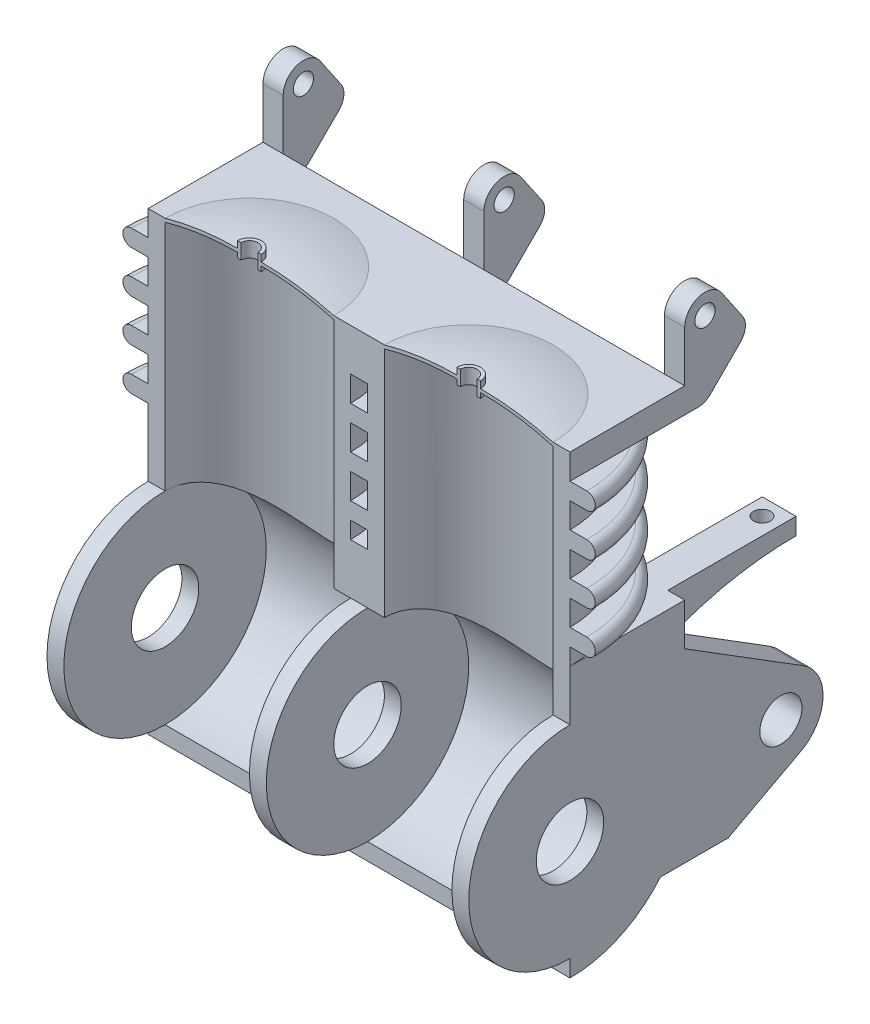
SolidWorks part; units mm, degrees
material "Plain Carbon Steel"
ref_plane "Front Plane" through (0, 0, 0) normal (0, 0, 1) x (1, 0, 0)
ref_plane "Top Plane" through (0, 0, 0) normal (0, 1, 0) x (1, 0, 0)
ref_plane "Right Plane" through (0, 0, 0) normal (1, 0, 0) x (0, 0, -1)
sketch "Sketch1" plane through (0, 0, 0) normal (1, 0, 0) x (0, 0, -1)
  line L1 (0, 160) -> (68, 160)
  line L2 (68, 160) -> (68, 86.6132)
  line L4 (0, 0) -> (0, 160)
  line L5 (0, 0) -> (70.0691, 0) construction
  arc A4 (0, 0) -> (68, 86.6132) centre (0, 70) ccw
  dimension "D3" = 70
  dimension "D1" = 160
  dimension "D2" = 68
extrude "Boss-Extrude1" add sketch "Sketch1" along normal mid plane 250
sketch "Sketch6" plane through (0, 0, 0) normal (0, 0, 1) x (1, 0, 0)
  line L0 (125, 160) -> (125, 170)
  line L3 (125, 195) -> (135, 195)
  line L7 (115, 267.9194) -> (115, 160)
  line L8 (115, 160) -> (125, 160)
  line L11 (125, 170) -> (135, 170)
  line L12 (135, 180) -> (125, 180)
  line L14 (135, 205) -> (125, 205)
  line L15 (65, 17.7772) -> (65, 302.2228) construction
  line L16 (125, 220) -> (135, 220)
  line L17 (135, 230) -> (125, 230)
  line L18 (125, 160) -> (125, 0) construction
  line L19 (125, 245) -> (135, 245)
  line L20 (135, 255) -> (125, 255)
  line L22 (125, 170) -> (125, 195) construction
  line L23 (125, 180) -> (125, 195)
  line L24 (125, 205) -> (125, 220)
  line L25 (125, 230) -> (125, 245)
  line L26 (125, 255) -> (125, 270)
  line L28 (125, 270) -> (115, 270)
  line L33 (72, 276.0033) -> (72, 280.0033)
  line L34 (72, 280.0033) -> (70, 280.0033)
  line L35 (70, 280.0033) -> (70, 271.0033)
  line L36 (70, 271.0033) -> (72, 271.0033)
  line L37 (72, 271.0033) -> (72, 274.0033)
  arc A2 (135, 170) -> (135, 180) centre (135, 175) ccw
  arc A3 (135, 195) -> (135, 205) centre (135, 200) ccw
  arc A4 (135, 220) -> (135, 230) centre (135, 225) ccw
  arc A5 (135, 245) -> (135, 255) centre (135, 250) ccw
  arc A6 (115, 270) -> (72, 276.0033) centre (72, 119.0033) ccw
  arc A7 (115, 267.9194) -> (72, 274.0033) centre (72, 119.0033) ccw
  arc A8 (114.4522, 268.0765) -> (72, 274.0033) centre (72, 119.0033) ccw construction
  point P23 (65, 160)
  dimension "D1" = 110
  dimension "D3" = 9
  dimension "D6" = 5
  dimension "D5" = 155
  dimension "D13" = 157
  dimension "D2" = 14
  dimension "D4" = 60
  dimension "D7" = 4
  dimension "D8" = 10
  dimension "D9" = 25
  dimension "D10" = 10
  dimension "D11" = 100
  dimension "D12" = 10
  dimension "D14" = 3
revolve "Revolve1" add sketch "Sketch6" angle 180 about L15
ref_plane "Plane1" through (0, 0, 0) normal (1, 0, 0) x (0, 0, -1)
sketch "Sketch14" plane through (125, 0, 0) normal (1, 0, 0) x (0, 0, -1)
  line L0 (0, 160) -> (0, 0) construction
  circle A0 centre (0, 70) radius 60
  dimension "D1" = 120
  dimension "D2" = 70
extrude "Cut-Extrude5" cut sketch "Sketch14" against normal through all
sketch "Sketch20" plane through (0, 160, 0) normal (0, 1, 0) x (1, 0, 0)
  line L0 (115, 0) -> (15, 0) construction
  circle A0 centre (65, 0) radius 50
  arc A1 (115, 0) -> (15, 0) centre (65, 0) ccw construction
extrude "Cut-Extrude6" cut sketch "Sketch20" against normal up to next
mirror "Mirror2" about plane through (0, 0, 0) normal (1, 0, 0) of "Revolve1", "Cut-Extrude6"
sketch "Sketch21" plane through (0, 0, 0) normal (0, 0, 1) x (1, 0, 0)
  line L0 (-162.1568, 70) -> (162.1568, 70) construction
  line L2 (-125, 130) -> (-115, 130) construction
  line L3 (125, 10) -> (-125, 10) construction
  line L4 (-125, 130) -> (-115, 130)
  line L5 (-115, 130) -> (-115, 90)
  line L6 (-115, 90) -> (-125, 90)
  line L7 (-125, 130) -> (-125, 10) construction
  line L8 (-125, 90) -> (-125, 130)
  line L9 (-5, 130) -> (5, 130)
  line L10 (5, 130) -> (5, 90)
  line L11 (5, 90) -> (-5, 90)
  line L12 (-5, 90) -> (-5, 130)
  line L13 (115, 130) -> (125, 130)
  line L14 (125, 130) -> (125, 90)
  line L15 (125, 90) -> (115, 90)
  line L16 (115, 90) -> (115, 130)
  line L17 (115, 130) -> (125, 130) construction
  line L19 (-15, 130) -> (15, 130) construction
  line L20 (0, 0) -> (0, 82.4628) construction
  line L21 (0, -88) -> (0, 88) construction
  point P3 (0, 70)
  dimension "D1" = 20
revolve "Revolve2" add sketch "Sketch21" angle 360 about L0
sketch "Sketch22" plane through (0, 270, 0) normal (0, 1, 0) x (1, 0, 0)
  line L0 (-125, 0) -> (-125, 68)
  line L1 (-125, 68) -> (125, 68)
  line L2 (125, 68) -> (125, 0)
  line L3 (5, 0) -> (-5, 0)
  arc A0 (125, 0) -> (5, 0) centre (65, 0) ccw
  arc A1 (-5, 0) -> (-125, 0) centre (-65, 0) ccw
extrude "Boss-Extrude4" add sketch "Sketch22" against normal up to vertex (15 mm away) up to point (0, 255, -25.9808)
sketch "Sketch23" plane through (125, 0, 0) normal (1, 0, 0) x (0, 0, -1)
  line L2 (102.2647, 288.6298) -> (89.9177, 306.7557)
  line L3 (68, 300) -> (68, 255)
  line L4 (68, 255) -> (68, 270) construction
  line L5 (68, 255) -> (76, 255)
  line L6 (83.0711, 257.9289) -> (101.0711, 275.9289)
  line L7 (36.0555, 255) -> (68, 255) construction
  arc A0 (89.9177, 306.7557) -> (68, 300) centre (80, 300) ccw
  circle A1 centre (80, 300) radius 6
  arc A2 (101.0711, 275.9289) -> (102.2647, 288.6298) centre (94, 283) ccw
  arc A3 (76, 255) -> (83.0711, 257.9289) centre (76, 265) ccw
  point P15 (80.1421, 255)
  dimension "D1" = 12
  dimension "D5" = 12
  dimension "D3" = 10
  dimension "D8" = 10
  dimension "D2" = 135
  dimension "D4" = 26
  dimension "D6" = 45
  dimension "D7" = 8
extrude "Boss-Extrude5" add sketch "Sketch23" against normal up to surface (250 mm away) up to face at (-125, 261, -34.4111)
ref_plane "Plane3" through (0, 0, -104) normal (0, 0, -1) x (-1, 0, 0)
sketch "Sketch25" plane through (0, 0, -104) normal (0, 0, -1) x (-1, 0, 0)
  line L0 (0, 0) -> (0, 365.3224) construction
  line L1 (-113, 312) -> (-6, 312)
  line L2 (-113, 312) -> (-113, 255)
  line L3 (-113, 255) -> (-6, 255)
  line L4 (-6, 312) -> (-6, 255)
  line L5 (6, 312) -> (113, 312)
  line L6 (6, 312) -> (6, 255)
  line L7 (6, 255) -> (113, 255)
  line L8 (113, 312) -> (113, 255)
  line L9 (0, 88) -> (0, -88) construction
  line L10 (125, 288.6298) -> (125, 306.7557) construction
  line L11 (125, 312) -> (-125, 312) construction
  line L12 (125, 255) -> (-125, 255) construction
  dimension "D1" = 12
  dimension "D2" = 12
extrude "Cut-Extrude8" cut sketch "Sketch25" against normal up to surface (36 mm away) up to face at (0, 285, -68)
ref_plane "Plane5" through (0, 231.9449, -133.9134) normal (0, 0.866, -0.5) x (1, 0, 0)
ref_plane "Plane6" through (115, 0, 0) normal (1, 0, 0) x (0, 0, -1)
sketch "Sketch32" plane through (115, 0, 0) normal (1, 0, 0) x (0, 0, -1)
  line L0 (68, 160) -> (143.9934, 160)
  line L1 (68, 86.6132) -> (68, 160) construction
  line L2 (143.9934, 160) -> (143.9934, 150)
  line L3 (68, 135) -> (68, 160)
  arc A0 (143.9934, 150) -> (68, 135) centre (143.9934, -50) ccw
  dimension "D2" = 200
  dimension "D1" = 10
  dimension "D3" = 25
extrude "Boss-Extrude8" add sketch "Sketch32" against normal blind 20
sketch "Sketch33" plane through (0, 160, 0) normal (0, 1, 0) x (1, 0, 0)
  line L0 (95, 143.9934) -> (115, 143.9934) construction
  circle A0 centre (104.8291, 133.9934) radius 5
  dimension "D1" = 10
  dimension "D2" = 10
extrude "Cut-Extrude12" cut sketch "Sketch33" against normal up to next
sketch "Sketch34" plane through (125, 0, 0) normal (1, 0, 0) x (0, 0, -1)
  line L0 (68, 135) -> (138.2269, 91.2144)
  line L1 (68, 86.6132) -> (68, 160) construction
  line L3 (68, 135) -> (68, 86.6132)
  line L4 (0, 70) -> (195.5172, 70) construction
  line L5 (53.619, 25) -> (93.7219, 25)
  line L6 (93.7219, 25) -> (136.7587, 47.938)
  arc A0 (143.9934, 150) -> (68, 135) centre (143.9934, -50) ccw construction
  arc A1 (138.2269, 91.2144) -> (136.7587, 47.938) centre (125, 70) cw
  arc A2 (0, 0) -> (68, 86.6132) centre (0, 70) ccw construction
  arc A3 (68, 86.6132) -> (53.619, 25) centre (0, 70) cw
  circle A4 centre (125, 70) radius 12.5
  dimension "D3" = 25
  dimension "D4" = 25
  dimension "D1" = 60
  dimension "D2" = 125
  dimension "D5" = 110
extrude "Boss-Extrude9" add sketch "Sketch34" against normal blind 20
mirror "Mirror3" about plane through (0, 0, 0) normal (1, 0, 0) of "Boss-Extrude9", "Cut-Extrude12", "Boss-Extrude8"
ref_plane "Plane7" through (0, 202.5, -116.9134) normal (0, 0.866, -0.5) x (-1, 0, 0)
